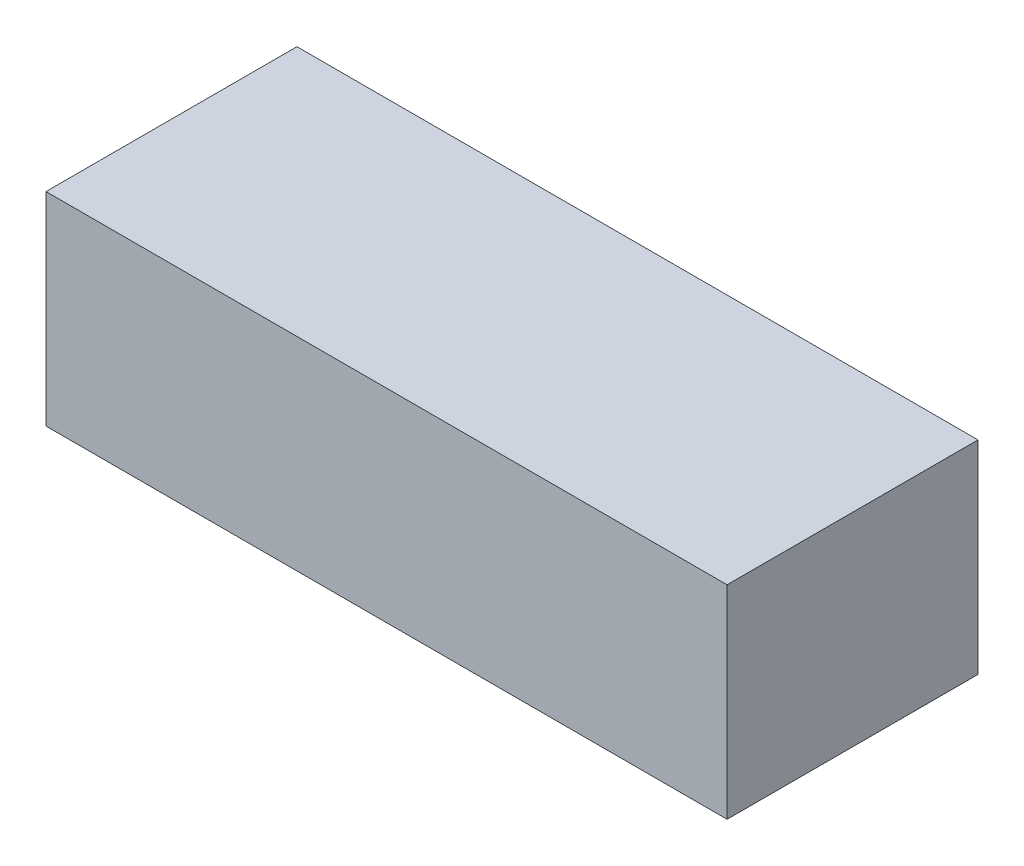
SolidWorks part; units mm, degrees
ref_plane "Alzado" through (0, 0, 0) normal (0, 0, 1) x (1, 0, 0)
ref_plane "Planta" through (0, 0, 0) normal (0, 1, 0) x (1, 0, 0)
ref_plane "Vista lateral" through (0, 0, 0) normal (1, 0, 0) x (0, 0, -1)
ref_plane "Plano1" through (0, 10, 0) normal (0, 1, 0) x (1, 0, 0)
sketch "Croquis1" plane through (0, 10, 0) normal (0, 1, 0) x (1, 0, 0)
  line L0 (46, -21) -> (46, 0)
  line L1 (46, 0) -> (-11, 0)
  line L2 (-11, 0) -> (-11, -21)
  line L3 (-11, -21) -> (46, -21)
extrude "Saliente-Extruir1" add sketch "Croquis1" against normal blind 17
sketch "Croquis2" plane through (0, -7, 0) normal (0, -1, 0) x (1, 0, 0)
  line L0 (45, 5) -> (-10, 5)
  line L1 (-10, 5) -> (-10, 16)
  line L2 (-10, 16) -> (45, 16)
  line L3 (45, 16) -> (45, 5)
extrude "Saliente-Extruir2" add sketch "Croquis2" along normal blind 1
sketch "Croquis3" plane through (0, -8, 0) normal (0, -1, 0) x (1, 0, 0)
  line L0 (44, 13) -> (44, 10)
  line L1 (44, 10) -> (-9, 10)
  line L2 (-9, 10) -> (-9, 13)
  line L3 (-9, 13) -> (44, 13)
extrude "Saliente-Extruir3" add sketch "Croquis3" along normal blind 1
